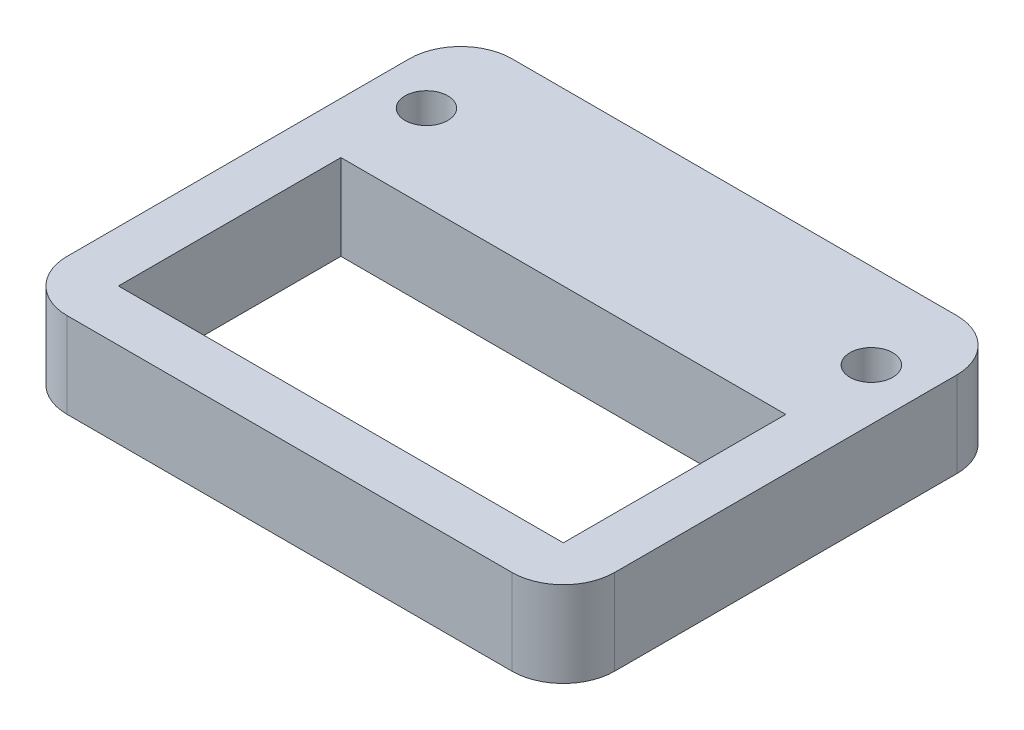
SolidWorks part; units mm, degrees
ref_plane "Front Plane" through (0, 0, 0) normal (0, 0, 1) x (1, 0, 0)
ref_plane "Top Plane" through (0, 0, 0) normal (0, 1, 0) x (1, 0, 0)
ref_plane "Right Plane" through (0, 0, 0) normal (1, 0, 0) x (0, 0, -1)
sketch "Sketch1" plane through (0, 0, 0) normal (0, 1, 0) x (1, 0, 0)
  line L1 (0, 0) -> (32, 0)
  line L2 (0, 0) -> (0, 26)
  line L3 (0, 26) -> (32, 26)
  line L4 (32, 0) -> (32, 26)
  line L5 (3, 3) -> (29, 3)
  line L6 (3, 3) -> (3, 16)
  line L7 (3, 16) -> (29, 16)
  line L8 (29, 3) -> (29, 16)
  circle A0 centre (3, 21) radius 1.25
  circle A1 centre (29, 21) radius 1.25
  point P13 (16, 3)
  point P14 (16, 0)
  dimension "D3" = 2.5
  dimension "D1" = 5
  dimension "D2" = 32
  dimension "D4" = 3
  dimension "D5" = 3
  dimension "D6" = 21
  dimension "D7" = 26
  dimension "D8" = 13
  dimension "D9" = 3
extrude "Boss-Extrude1" add sketch "Sketch1" along normal blind 5
fillet "Fillet1" radius 3 4 edges at (0, 2.5, -26) (32, 2.5, -26) (0, 2.5, 0) (32, 2.5, 0)
